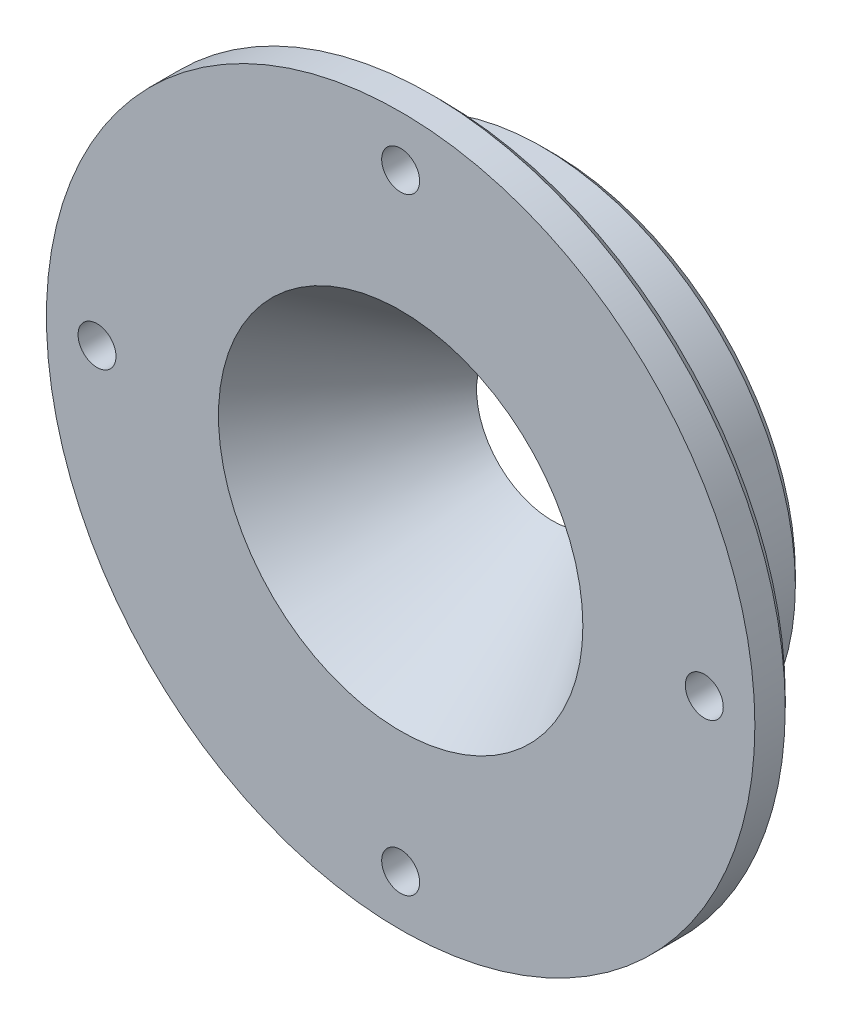
SolidWorks part; units mm, degrees
material "6061 Alloy"
ref_plane "Front Plane" through (0, 0, 0) normal (0, 0, 1) x (1, 0, 0)
ref_plane "Top Plane" through (0, 0, 0) normal (0, 1, 0) x (1, 0, 0)
ref_plane "Right Plane" through (0, 0, 0) normal (1, 0, 0) x (0, 0, -1)
sketch "Sketch1" plane through (0, 0, 0) normal (1, 0, 0) x (0, 0, -1)
  line L0 (-18.4542, 0) -> (17.5519, 0) construction
  line L1 (0, 22.864) -> (19.05, 9.525)
  line L2 (19.05, 9.525) -> (19.05, 31.75)
  line L3 (19.05, 31.75) -> (5.08, 31.75)
  line L4 (5.08, 31.75) -> (5.08, 44.45)
  line L5 (5.08, 44.45) -> (0, 44.45)
  line L6 (0, 44.45) -> (0, 22.864)
  dimension "D1" = 19.05
  dimension "D2" = 5.08
  dimension "D3" = 44.45
  dimension "D4" = 31.75
  dimension "D5" = 9.525
  dimension "D6" = 35
revolve "Revolve1" add sketch "Sketch1" angle 360 about L0
hole_wizard "3/16 (0.1875) Diameter Hole1" positions "Sketch2" profile "Sketch3" hole size "3/16" standard "ANSI Inch" end condition through all
sketch "Sketch2" plane through (0, 0, 0) normal (0, 0, 1) x (1, 0, 0)
  point P0 (0, 38.1)
  point P9 (38.1, 0)
  point P10 (0, -38.1)
  point P11 (-38.1, 0)
  point P12 (0, 0)
  dimension "D1" = 38.1
  dimension "D2" = 4
sketch "Sketch3" plane through (0, 38.1, 0) normal (1, 0, 0) x (0, -1, 0)
  line L0 (0, 0) -> (0, 19.05)
  line L1 (0, 19.05) -> (2.3812, 19.05)
  line L2 (2.3812, 19.05) -> (2.3812, 0)
  line L5 (2.3812, 0) -> (0, 0)
  line L11 (0, -6.35) -> (0, 107.95) construction
  dimension "Thru Hole Dia." = 4.7625
  dimension "Thru Hole Depth" = 19.05
fillet "Fillet1" radius 2.54 1 edges at (31.75, 0, -5.08)
chamfer "Chamfer1" distance 1.27 angle 45 2 edges at (31.75, 0, -19.05) (44.45, 0, -5.08)
